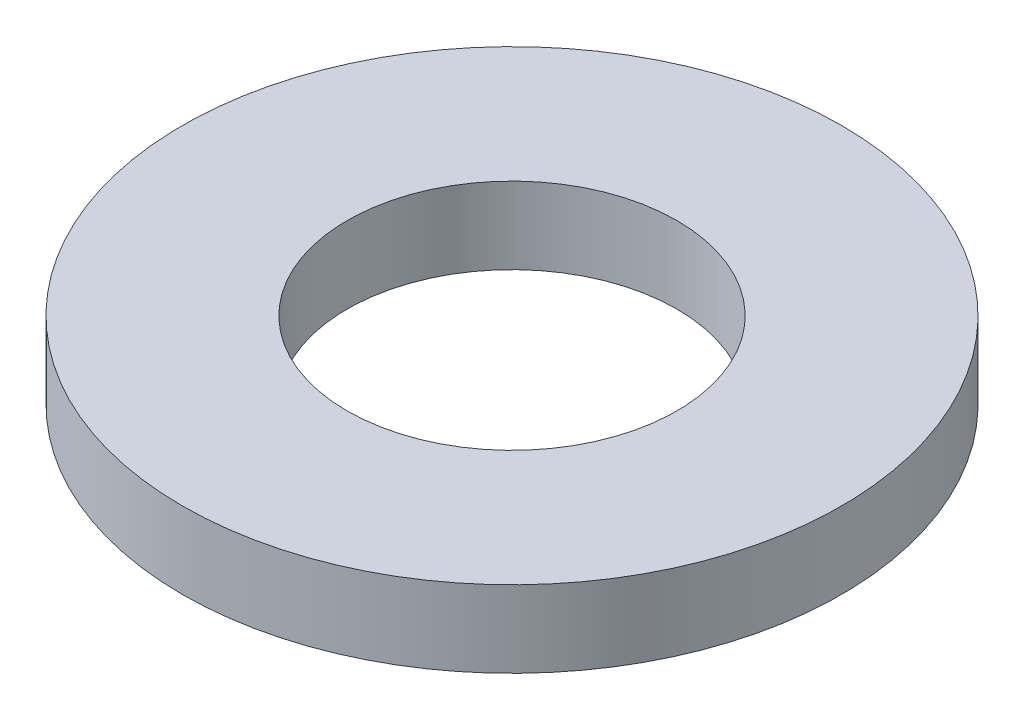
SolidWorks part; units mm, degrees
ref_plane "Front Plane" through (0, 0, 0) normal (0, 0, 1) x (1, 0, 0)
ref_plane "Top Plane" through (0, 0, 0) normal (0, 1, 0) x (1, 0, 0)
ref_plane "Right Plane" through (0, 0, 0) normal (1, 0, 0) x (0, 0, -1)
sketch "Sketch1" plane through (0, 0, 0) normal (0, 1, 0) x (1, 0, 0)
  circle A0 centre (0, 0) radius 8.7312
  dimension "OD" = 17.4625
extrude "Boss-Extrude1" add sketch "Sketch1" along normal blind 2.032
sketch "Sketch5" plane through (0, 2.032, 0) normal (0, 1, 0) x (-1, 0, 0)
  circle A0 centre (0, 0) radius 4.3688
  dimension "ID" = 8.7376
extrude "Cut-Extrude1" cut sketch "Sketch5" against normal through all
